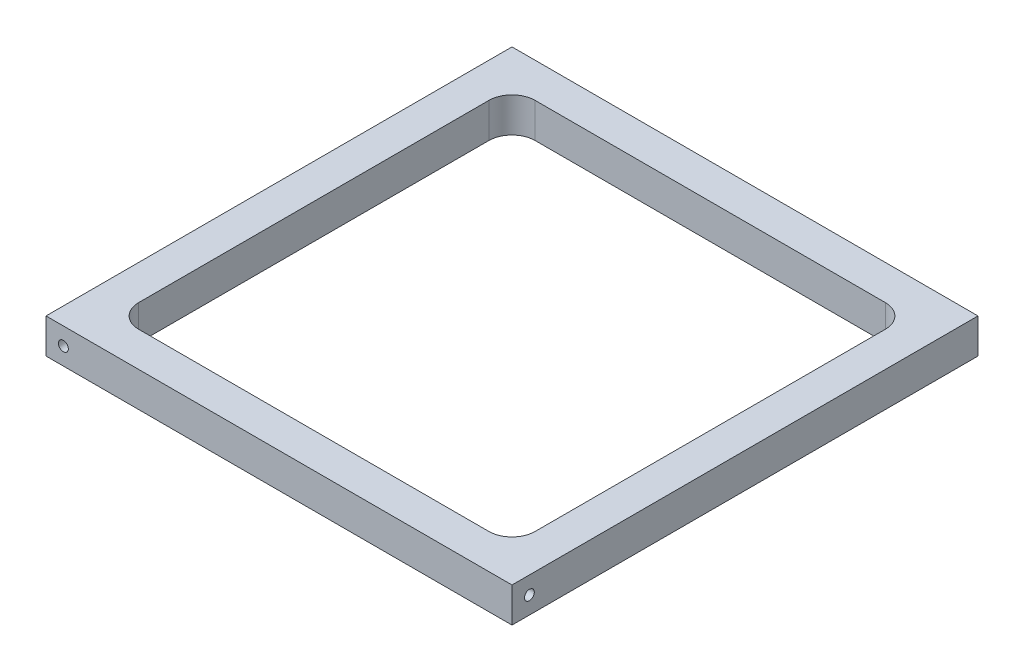
SolidWorks part; units mm, degrees
material "6061-T6 (SS)"
ref_plane "Front Plane" through (0, 0, 0) normal (0, 0, 1) x (1, 0, 0)
ref_plane "Top Plane" through (0, 0, 0) normal (0, 1, 0) x (1, 0, 0)
ref_plane "Right Plane" through (0, 0, 0) normal (1, 0, 0) x (0, 0, -1)
sketch "Sketch1" plane through (0, 0, 0) normal (0, 1, 0) x (1, 0, 0)
  line L5 (0, 0) -> (127.635, 0)
  line L6 (0, 0) -> (0, 127.635)
  line L7 (0, 127.635) -> (127.635, 127.635)
  line L8 (127.635, 0) -> (127.635, 127.635)
  dimension "D1" = 127.635
  dimension "D2" = 127.635
extrude "Boss-Extrude1" add sketch "Sketch1" along normal blind 9.525 contours L5 L8 L7 L6
sketch "Sketch5" plane through (0, 9.525, 0) normal (0, 1, 0) x (1, 0, 0)
  line L0 (63.8175, 127.635) -> (63.8175, 0) construction
  line L1 (0, 127.635) -> (127.635, 127.635) construction
  line L2 (0, 0) -> (127.635, 0) construction
  line L4 (9.525, 118.11) -> (118.11, 118.11)
  line L5 (9.525, 118.11) -> (9.525, 9.525)
  line L6 (9.525, 9.525) -> (118.11, 9.525)
  line L7 (118.11, 118.11) -> (118.11, 9.525)
  line L8 (9.525, 118.11) -> (118.11, 9.525) construction
  line L9 (9.525, 9.525) -> (118.11, 118.11) construction
  point P6 (63.8175, 63.8175)
  dimension "D1" = 108.585
  dimension "D2" = 108.585
extrude "Cut-Extrude1" cut sketch "Sketch5" against normal blind 9.525 contours L5 L4 L7 L6
fillet "Fillet1" radius 6.35 4 edges at (118.11, 4.7625, -9.525) (118.11, 4.7625, -118.11) (9.525, 4.7625, -118.11) (9.525, 4.7625, -9.525)
sketch "Sketch6" plane through (127.635, 0, 0) normal (1, 0, 0) x (0, 0, -1)
  line L0 (0, 9.525) -> (0, 0) construction
  line L1 (0, 0) -> (127.635, 0) construction
  point P0 (4.7625, 4.7625)
  dimension "D1" = 4.7625
  dimension "D2" = 4.7625
hole_wizard "Tap Drill for #6-32 Tap2" positions "Sketch9" profile "Sketch10" hole size "#6-32" standard "ANSI Inch"
sketch "Sketch9" plane through (127.635, 0, 0) normal (1, 0, 0) x (0, 0, -1)
  point P0 (4.7625, 4.7625)
sketch "Sketch10" plane through (127.635, 4.7625, -4.7625) normal (0, 1, 0) x (0, 0, -1)
  line L0 (0, 0) -> (0, 13.5127)
  line L1 (0, 13.5127) -> (1.3525, 12.7)
  line L2 (1.3525, 12.7) -> (1.3525, 0)
  line L5 (1.3525, 0) -> (0, 0)
  line L10 (0, 13.5127) -> (-1.3525, 12.7) construction
  line L11 (0, -6.35) -> (0, 107.95) construction
  dimension "Hole Dia." = 2.7051
  dimension "Hole Depth" = 12.7
  dimension "Drill Angle" = 118
sketch "Sketch11" plane through (0, 0, 0) normal (0, 0, 1) x (1, 0, 0)
  line L0 (0, 9.525) -> (0, 0) construction
  line L1 (0, 9.525) -> (127.635, 9.525) construction
  point P0 (4.7625, 4.7625)
  dimension "D1" = 4.7625
  dimension "D2" = 4.7625
hole_wizard "Tap Drill for #6-32 Tap3" positions "Sketch14" profile "Sketch15" hole size "#6-32" standard "ANSI Inch"
sketch "Sketch14" plane through (0, 0, 0) normal (0, 0, 1) x (1, 0, 0)
  point P0 (4.7625, 4.7625)
sketch "Sketch15" plane through (4.7625, 4.7625, 0) normal (1, 0, 0) x (0, -1, 0)
  line L0 (0, 0) -> (0, 13.5127)
  line L1 (0, 13.5127) -> (1.3525, 12.7)
  line L2 (1.3525, 12.7) -> (1.3525, 0)
  line L5 (1.3525, 0) -> (0, 0)
  line L10 (0, 13.5127) -> (-1.3525, 12.7) construction
  line L11 (0, -6.35) -> (0, 107.95) construction
  dimension "Hole Dia." = 2.7051
  dimension "Hole Depth" = 12.7
  dimension "Drill Angle" = 118
sketch "Sketch16" plane through (0, 0, 0) normal (-1, 0, 0) x (0, 0, 1)
  line L0 (-127.635, 9.525) -> (-127.635, 0) construction
  line L1 (0, 9.525) -> (-127.635, 9.525) construction
  point P0 (-122.8725, 4.7625)
  dimension "D1" = 4.7625
  dimension "D2" = 4.7625
hole_wizard "Tap Drill for #6-32 Tap4" positions "Sketch17" profile "Sketch18" hole size "#6-32" standard "ANSI Inch"
sketch "Sketch17" plane through (0, 0, 0) normal (-1, 0, 0) x (0, 0, 1)
  point P0 (-122.8725, 4.7625)
sketch "Sketch18" plane through (0, 4.7625, -122.8725) normal (0, 1, 0) x (0, 0, 1)
  line L0 (0, 0) -> (0, 13.5127)
  line L1 (0, 13.5127) -> (1.3525, 12.7)
  line L2 (1.3525, 12.7) -> (1.3525, 0)
  line L5 (1.3525, 0) -> (0, 0)
  line L10 (0, 13.5127) -> (-1.3525, 12.7) construction
  line L11 (0, -6.35) -> (0, 107.95) construction
  dimension "Hole Dia." = 2.7051
  dimension "Hole Depth" = 12.7
  dimension "Drill Angle" = 118
sketch "Sketch19" plane through (0, 0, -127.635) normal (0, 0, -1) x (-1, 0, 0)
  line L0 (-127.635, 9.525) -> (-127.635, 0) construction
  line L1 (0, 9.525) -> (-127.635, 9.525) construction
  point P0 (-122.8725, 4.7625)
  dimension "D1" = 4.7625
  dimension "D2" = 4.7625
hole_wizard "Tap Drill for #6-32 Tap5" positions "Sketch20" profile "Sketch21" hole size "#6-32" standard "ANSI Inch"
sketch "Sketch20" plane through (0, 0, -127.635) normal (0, 0, -1) x (-1, 0, 0)
  point P0 (-122.8725, 4.7625)
sketch "Sketch21" plane through (122.8725, 4.7625, -127.635) normal (1, 0, 0) x (0, 1, 0)
  line L0 (0, 0) -> (0, 13.5127)
  line L1 (0, 13.5127) -> (1.3525, 12.7)
  line L2 (1.3525, 12.7) -> (1.3525, 0)
  line L5 (1.3525, 0) -> (0, 0)
  line L10 (0, 13.5127) -> (-1.3525, 12.7) construction
  line L11 (0, -6.35) -> (0, 107.95) construction
  dimension "Hole Dia." = 2.7051
  dimension "Hole Depth" = 12.7
  dimension "Drill Angle" = 118
